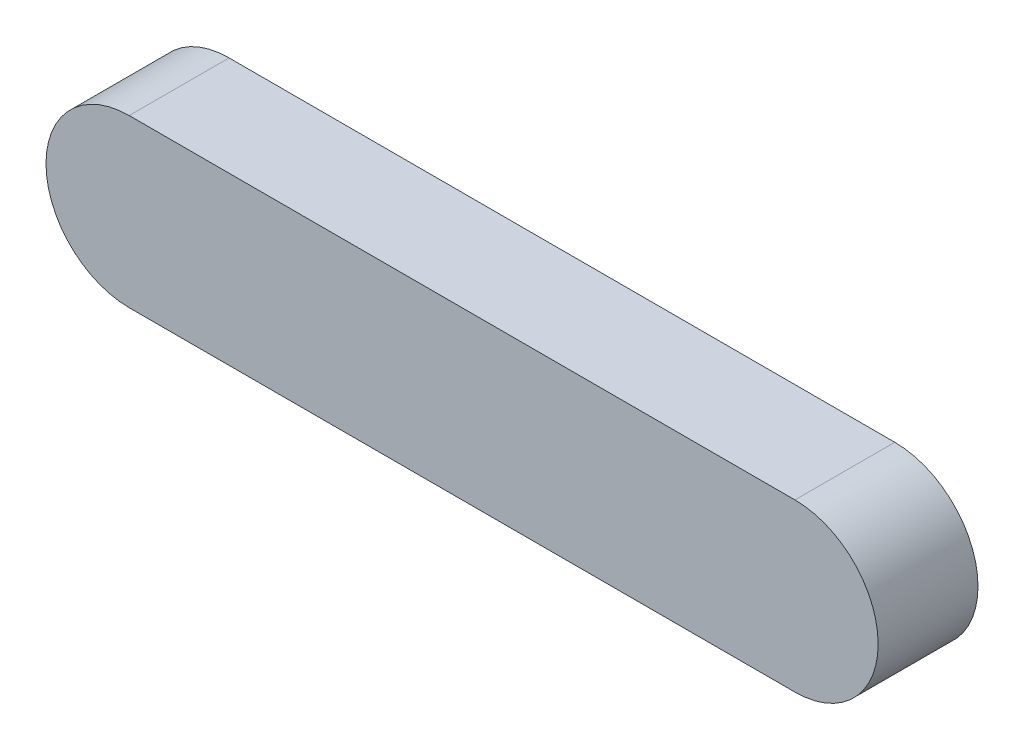
SolidWorks part; units mm, degrees
ref_plane "Front Plane" through (0, 0, 0) normal (0, 0, 1) x (1, 0, 0)
ref_plane "Top Plane" through (0, 0, 0) normal (0, 1, 0) x (1, 0, 0)
ref_plane "Right Plane" through (0, 0, 0) normal (1, 0, 0) x (0, 0, -1)
sketch "Sketch1" plane through (0, 0, 0) normal (0, 0, 1) x (1, 0, 0)
  line L0 (0, 0) -> (40, 0) construction
  line L1 (0, 5) -> (40, 5)
  line L2 (0, -5) -> (40, -5)
  arc A0 (0, 5) -> (0, -5) centre (0, 0) ccw
  arc A1 (40, -5) -> (40, 5) centre (40, 0) ccw
  point P3 (20, 0)
  dimension "D1" = 5
  dimension "D2" = 40
extrude "Boss-Extrude1" add sketch "Sketch1" along normal blind 6
